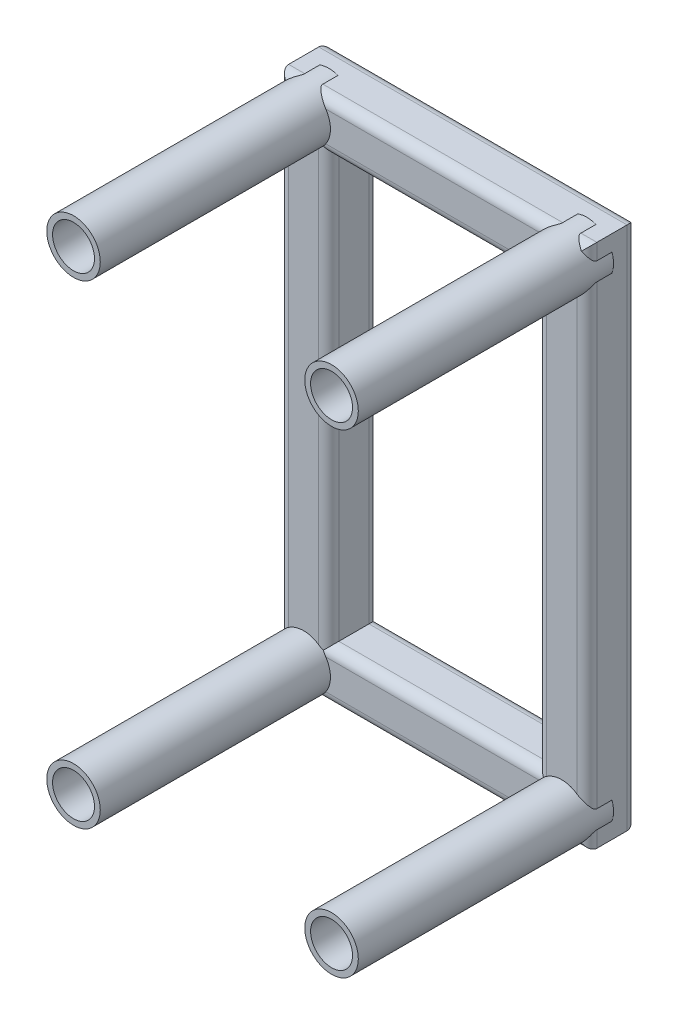
SolidWorks part; units mm, degrees
ref_plane "Front Plane" through (0, 0, 0) normal (0, 0, 1) x (1, 0, 0)
ref_plane "Top Plane" through (0, 0, 0) normal (0, 1, 0) x (1, 0, 0)
ref_plane "Right Plane" through (0, 0, 0) normal (1, 0, 0) x (0, 0, -1)
sketch3d "3DSketch1"
  line L0 (-51.3487, 94.4354, 0) -> (-51.3487, 94.4354, 101.6)
  line L1 (-51.3487, 94.4354, 0) -> (51.3487, 94.4354, 0)
  line L2 (-51.3487, 94.4354, 0) -> (-51.3487, -94.4354, 0)
  line L3 (-51.3487, -94.4354, 0) -> (51.3487, -94.4354, 0)
  line L4 (51.3487, 94.4354, 0) -> (51.3487, -94.4354, 0)
  line L5 (-51.3487, 94.4354, 0) -> (51.3487, -94.4354, 0) construction
  line L6 (-51.3487, -94.4354, 0) -> (51.3487, 94.4354, 0) construction
  line L7 (-51.3487, -94.4354, 0) -> (-51.3487, -94.4354, 101.6)
  line L8 (51.3487, 94.4354, 0) -> (51.3487, 94.4354, 101.6)
  line L9 (51.3487, -94.4354, 0) -> (51.3487, -94.4354, 101.6)
  point P0 (0, 0, 0)
  dimension "D1" = 101.6
other "Structural Member1"
ref_plane "Plane1" through (-51.3487, 94.4354, 0) normal (0, -1, 0) x (1, 0, 0)
sketch "Sketch18" plane through (-51.3487, 94.4354, 0) normal (0, -1, 0) x (1, 0, 0)
  line L0 (-6, -8) -> (6, -8)
  line L1 (-8, -6) -> (-8, 6)
  line L2 (6, 8) -> (-6, 8)
  line L3 (8, 6) -> (8, -6)
  line L4 (-6, -10) -> (6, -10)
  line L5 (-10, -6) -> (-10, 6)
  line L6 (6, 10) -> (-6, 10)
  line L7 (10, 6) -> (10, -6)
  arc A0 (10, 6) -> (6, 10) centre (6, 6) ccw
  arc A1 (6, -10) -> (10, -6) centre (6, -6) ccw
  arc A2 (-10, -6) -> (-6, -10) centre (-6, -6) ccw
  arc A3 (-6, 10) -> (-10, 6) centre (-6, 6) ccw
  arc A4 (-6, 8) -> (-8, 6) centre (-6, 6) ccw
  arc A5 (8, 6) -> (6, 8) centre (6, 6) ccw
  arc A6 (6, -8) -> (8, -6) centre (6, -6) ccw
  arc A7 (-8, -6) -> (-6, -8) centre (-6, -6) ccw
  point P0 (-10, 0)
  point P1 (10, 0)
  point P2 (0, 10)
  point P3 (0, -10)
  point P4 (0, 0)
  point P5 (-10, -10)
  point P6 (10, -10)
  point P7 (10, 10)
  point P8 (-10, 10)
  point P33 (0, 0)
  dimension "D1" = 4
  dimension "Thickness" = 2
  dimension "V_leg" = 20
other "Structural Member2"
ref_plane "Plane2" through (-51.3487, 94.4354, 0) normal (0, 0, 1) x (1, 0, 0)
sketch "Sketch19" plane through (-51.3487, 94.4354, 0) normal (0, 0, 1) x (1, 0, 0)
  circle A0 centre (0, 0) radius 8.35
  circle A1 centre (0, 0) radius 10.65
  point P3 (0, 0)
  dimension "In_dia" = 16.7
  dimension "Out_dia" = 21.3
